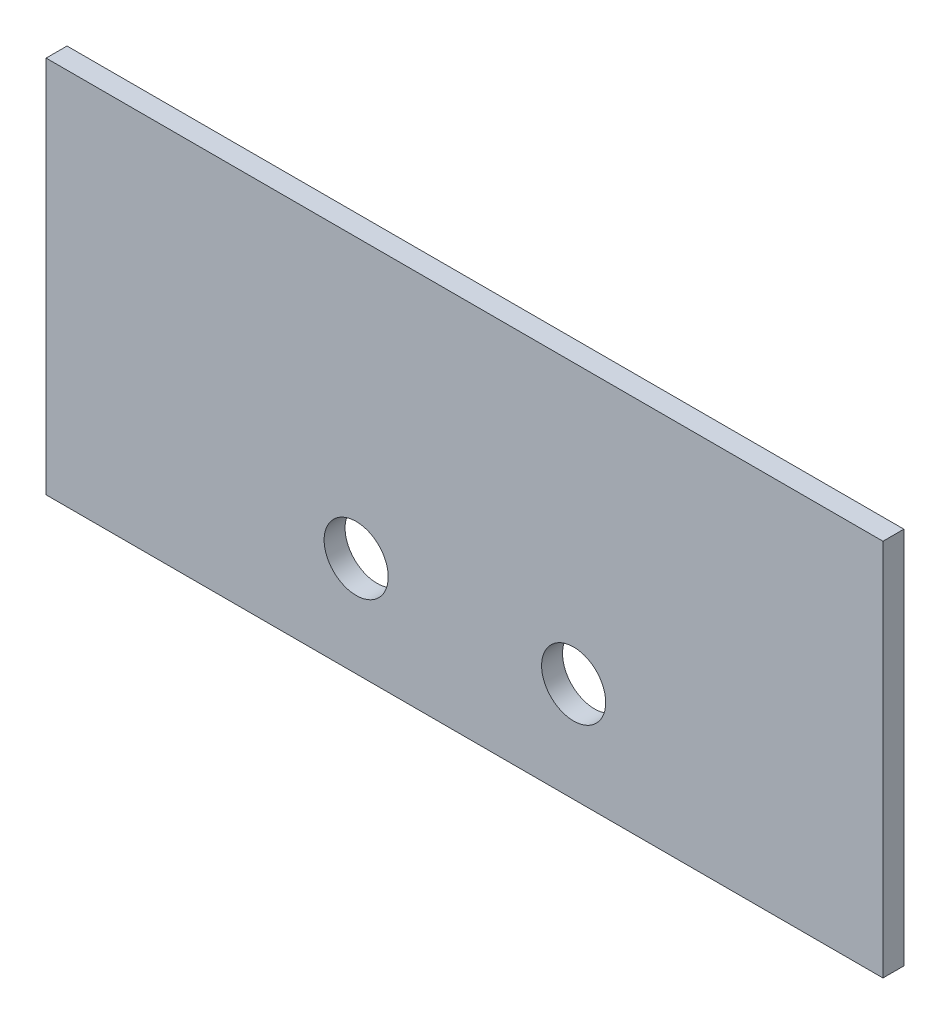
SolidWorks part; units mm, degrees
ref_plane "Front Plane" through (0, 0, 0) normal (0, 0, 1) x (1, 0, 0)
ref_plane "Top Plane" through (0, 0, 0) normal (0, 1, 0) x (1, 0, 0)
ref_plane "Right Plane" through (0, 0, 0) normal (1, 0, 0) x (0, 0, -1)
sketch "Sketch1" plane through (0, 0, 0) normal (0, 0, 1) x (1, 0, 0)
  line L2 (0, 0) -> (127, 0)
  line L3 (0, 0) -> (0, 57.404)
  line L4 (0, 57.404) -> (127, 57.404)
  line L7 (127, 0) -> (127, 57.404)
  circle A0 centre (80.056, 15.167) radius 4.864 construction
  circle A1 centre (47.056, 15.167) radius 4.864 construction
  circle A2 centre (80.056, 15.167) radius 4.864
  circle A3 centre (47.056, 15.167) radius 4.864
  dimension "D1" = 57.404
  dimension "D2" = 127
extrude "Boss-Extrude1" add sketch "Sketch1" along normal blind 3.175
